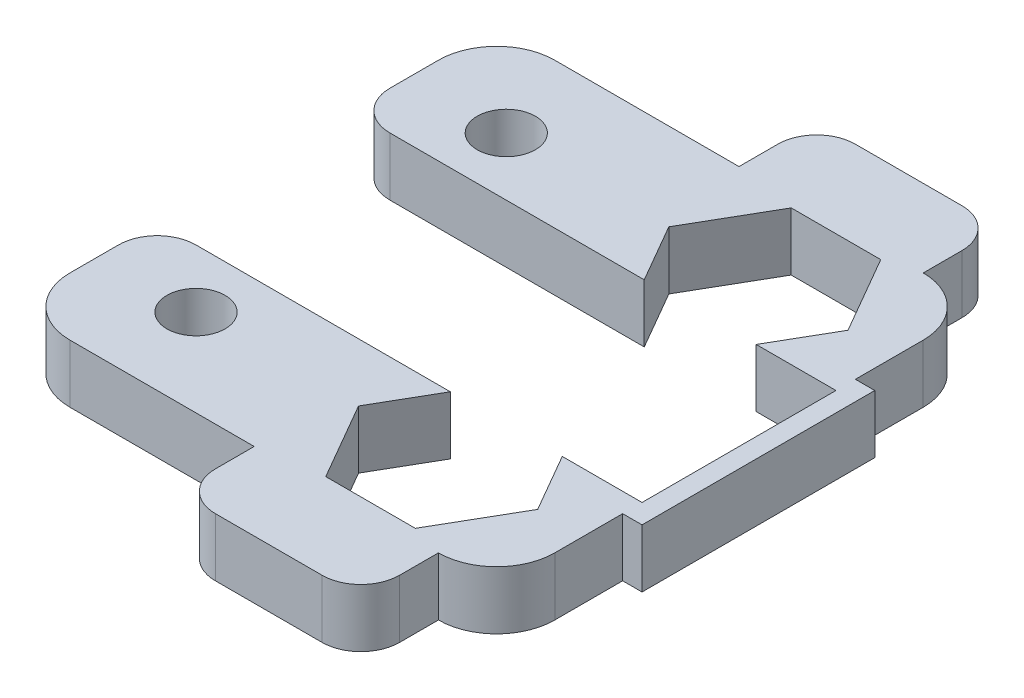
SolidWorks part; units mm, degrees
ref_plane "Front Plane" through (0, 0, 0) normal (0, 0, 1) x (1, 0, 0)
ref_plane "Top Plane" through (0, 0, 0) normal (0, 1, 0) x (1, 0, 0)
ref_plane "Right Plane" through (0, 0, 0) normal (1, 0, 0) x (0, 0, -1)
sketch "Sketch3" plane through (0, 0, 0) normal (0, 1, 0) x (1, 0, 0)
  line L0 (-60.7457, 16.9789) -> (-60.7457, 18.9789)
  line L1 (-52.3589, 9.4789) -> (-48.2457, 9.4789)
  line L2 (-50.6269, 12.4789) -> (-52.9363, 16.4789)
  line L3 (-52.9363, 16.4789) -> (-57.5551, 16.4789)
  line L4 (-57.5551, 16.4789) -> (-59.8645, 12.4789)
  line L5 (-59.8645, 12.4789) -> (-58.1324, 9.4789)
  line L7 (-71.2457, 9.4789) -> (-58.1324, 9.4789)
  line L8 (-70.2457, 16.9789) -> (-60.7457, 16.9789)
  line L9 (-73.2457, 13.9789) -> (-73.2457, 11.4789)
  line L10 (-58.7457, 20.9789) -> (-53.2457, 20.9789)
  line L11 (-51.2457, 18.9789) -> (-51.2457, 16.9789)
  line L12 (-60.7457, -8.0211) -> (-60.7457, -10.0211)
  line L13 (-58.7457, -12.0211) -> (-53.2457, -12.0211)
  line L14 (-51.2457, -10.0211) -> (-51.2457, -8.0211)
  line L15 (-52.3589, 9.4789) -> (-50.6269, 12.4789)
  line L16 (-50.6269, -3.5211) -> (-52.3589, -0.5211)
  line L18 (-58.1324, -0.5211) -> (-59.8645, -3.5211)
  line L19 (-70.2457, -8.0211) -> (-60.7457, -8.0211)
  line L20 (-48.2457, 13.9789) -> (-48.2457, 10.4789)
  line L21 (-73.2457, 16.9789) -> (-48.2457, -8.0211) construction
  line L22 (-73.2457, -8.0211) -> (-48.2457, 16.9789) construction
  line L23 (-71.2457, -0.5211) -> (-58.1324, -0.5211)
  line L24 (-48.2457, 10.4789) -> (-47.2457, 10.4789)
  line L25 (-47.2457, 10.4789) -> (-47.2457, -1.5211)
  line L26 (-47.2457, -1.5211) -> (-48.2457, -1.5211)
  line L27 (-48.2457, 9.4789) -> (-48.2457, -0.5211)
  line L28 (-48.2457, -1.5211) -> (-48.2457, -5.0211)
  line L29 (-73.2457, -2.5211) -> (-73.2457, -5.0211)
  line L30 (-59.8645, -3.5211) -> (-57.5551, -7.5211)
  line L31 (-57.5551, -7.5211) -> (-52.9363, -7.5211)
  line L32 (-52.9363, -7.5211) -> (-50.6269, -3.5211)
  line L33 (-52.3589, -0.5211) -> (-48.2457, -0.5211)
  line L34 (-56.7457, 0.4789) -> (-57.5551, 0.4789) [skipped]
  line L35 (-57.5551, 8.4789) -> (-56.7457, 8.4789) [skipped]
  arc A1 (-58.7457, -12.0211) -> (-60.7457, -10.0211) centre (-58.7457, -10.0211) cw
  arc A2 (-53.2457, -12.0211) -> (-51.2457, -10.0211) centre (-53.2457, -10.0211) ccw
  arc A3 (-51.2457, 18.9789) -> (-53.2457, 20.9789) centre (-53.2457, 18.9789) ccw
  arc A4 (-60.7457, 18.9789) -> (-58.7457, 20.9789) centre (-58.7457, 18.9789) cw
  circle A10 centre (-68.2457, -3.5211) radius 1.5
  circle A11 centre (-68.2457, 12.4789) radius 1.5
  arc A12 (-48.2457, 13.9789) -> (-51.2457, 16.9789) centre (-51.2457, 13.9789) ccw
  arc A13 (-51.2457, -8.0211) -> (-48.2457, -5.0211) centre (-51.2457, -5.0211) ccw
  arc A14 (-70.2457, -8.0211) -> (-73.2457, -5.0211) centre (-70.2457, -5.0211) cw
  arc A15 (-73.2457, 13.9789) -> (-70.2457, 16.9789) centre (-70.2457, 13.9789) cw
  arc A16 (-73.2457, -2.5211) -> (-71.2457, -0.5211) centre (-71.2457, -2.5211) cw
  arc A17 (-73.2457, 11.4789) -> (-71.2457, 9.4789) centre (-71.2457, 11.4789) ccw
  point P15 (-60.7457, -12.0211)
  point P22 (-60.7457, 20.9789)
  point P23 (-60.7457, 4.4789)
  point P71 (-73.2457, -0.5211)
  dimension "D3" = 3
  dimension "D5" = 4
  dimension "D6" = 4
  dimension "D7" = 2
  dimension "D10" = 25
  dimension "D13" = 25
  dimension "D24" = 3
  dimension "D25" = 2
  dimension "D14" = 10
  dimension "D15" = 7.5
  dimension "D21" = 1
  dimension "D22" = 1
  dimension "D23" = 1
extrude "Boss-Extrude1" add sketch "Sketch3" along normal blind 3
